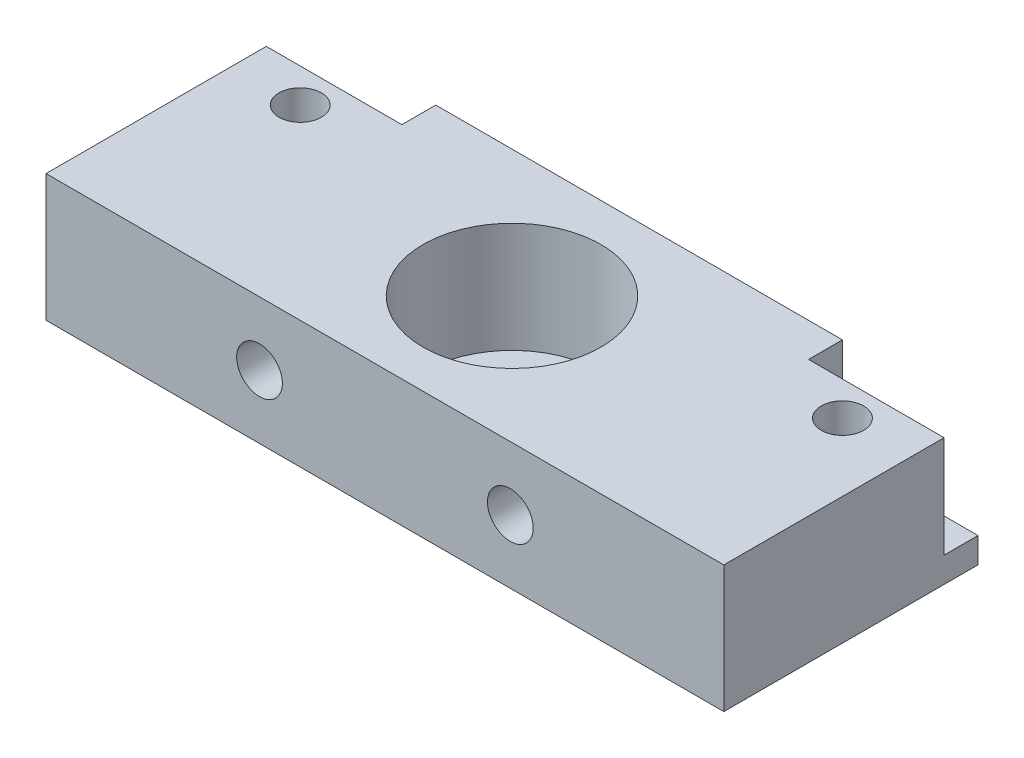
SolidWorks part; units mm, degrees
ref_plane "Front Plane" through (0, 0, 0) normal (0, 0, 1) x (1, 0, 0)
ref_plane "Top Plane" through (0, 0, 0) normal (0, 1, 0) x (1, 0, 0)
ref_plane "Right Plane" through (0, 0, 0) normal (1, 0, 0) x (0, 0, -1)
sketch "Sketch1" plane through (0, 0, 0) normal (0, 1, 0) x (1, 0, 0)
  line L1 (-37.8815, 10.7766) -> (63.7185, 10.7766)
  line L2 (-37.8815, 10.7766) -> (-37.8815, -27.3234)
  line L3 (-37.8815, -27.3234) -> (63.7185, -27.3234)
  line L4 (63.7185, 10.7766) -> (63.7185, -27.3234)
  dimension "D1" = 101.6
  dimension "D2" = 38.1
extrude "Boss-Extrude1" add sketch "Sketch1" along normal blind 19.05
sketch "Sketch2" plane through (0, 19.05, 0) normal (0, 1, 0) x (1, 0, 0)
  line L0 (-37.8815, 10.7766) -> (-37.8815, -27.3234) construction
  line L1 (63.7185, -27.3234) -> (63.7185, 10.7766) construction
  line L2 (63.7185, 10.7766) -> (-37.8815, 10.7766) construction
  circle A0 centre (-27.7215, 0.6166) radius 3.175
  circle A1 centre (53.5585, 0.6166) radius 3.175
  dimension "D3" = 10.16
  dimension "D5" = 6.35
  dimension "D6" = 6.35
  dimension "D1" = 10.16
  dimension "D2" = 10.16
  dimension "D4" = 10.16
extrude "Cut-Extrude1" cut sketch "Sketch2" against normal blind 16.51
sketch "Sketch3" plane through (0, 0, 27.3234) normal (0, 0, 1) x (1, 0, 0)
  line L0 (-37.8815, 19.05) -> (-37.8815, 0) construction
  line L1 (-37.8815, 0) -> (63.7185, 0) construction
  circle A0 centre (-5.8775, 9.525) radius 3.429
  circle A1 centre (31.7145, 9.525) radius 3.429
  dimension "D5" = 6.858
  dimension "D6" = 6.858
  dimension "D1" = 37.592
  dimension "D2" = 32.004
  dimension "D3" = 9.525
  dimension "D4" = 9.525
extrude "Cut-Extrude2" cut sketch "Sketch3" against normal up to next
sketch "Sketch4" plane through (0, 19.05, 0) normal (0, 1, 0) x (1, 0, 0)
  line L0 (-37.8815, 10.7766) -> (-37.8815, -27.3234) construction
  line L1 (63.7185, 10.7766) -> (-37.8815, 10.7766) construction
  circle A0 centre (12.9185, -8.2734) radius 13.335
  dimension "D3" = 26.67
  dimension "D1" = 50.8
  dimension "D2" = 19.05
extrude "Cut-Extrude3" cut sketch "Sketch4" against normal blind 16.51
sketch "Sketch5" plane through (0, 19.05, 0) normal (0, 1, 0) x (1, 0, 0)
  line L0 (-37.8815, 10.7766) -> (-37.8815, -27.3234) construction
  line L1 (63.7185, 10.7766) -> (-37.8815, 10.7766) construction
  circle A0 centre (12.9185, -8.2734) radius 3.556
  dimension "D3" = 7.112
  dimension "D1" = 50.8
  dimension "D2" = 19.05
extrude "Cut-Extrude4" cut sketch "Sketch5" against normal through all
sketch "Sketch6" plane through (0, 19.05, 0) normal (0, 1, 0) x (1, 0, 0)
  line L0 (63.7185, 10.7766) -> (-37.8815, 10.7766) construction
  line L1 (-17.5615, 10.7766) -> (-37.8815, 10.7766)
  line L2 (-17.5615, 10.7766) -> (-17.5615, 5.6966)
  line L3 (-17.5615, 5.6966) -> (-37.8815, 5.6966)
  line L4 (-37.8815, 10.7766) -> (-37.8815, 5.6966)
  line L5 (-37.8815, 10.7766) -> (-37.8815, -27.3234) construction
  line L7 (63.7185, 10.7766) -> (43.3985, 10.7766)
  line L8 (63.7185, 10.7766) -> (63.7185, 5.6966)
  line L9 (63.7185, 5.6966) -> (43.3985, 5.6966)
  line L10 (43.3985, 10.7766) -> (43.3985, 5.6966)
  dimension "D1" = 20.32
  dimension "D2" = 20.32
  dimension "D3" = 5.08
  dimension "D4" = 5.08
extrude "Cut-Extrude5" cut sketch "Sketch6" against normal blind 15.24
